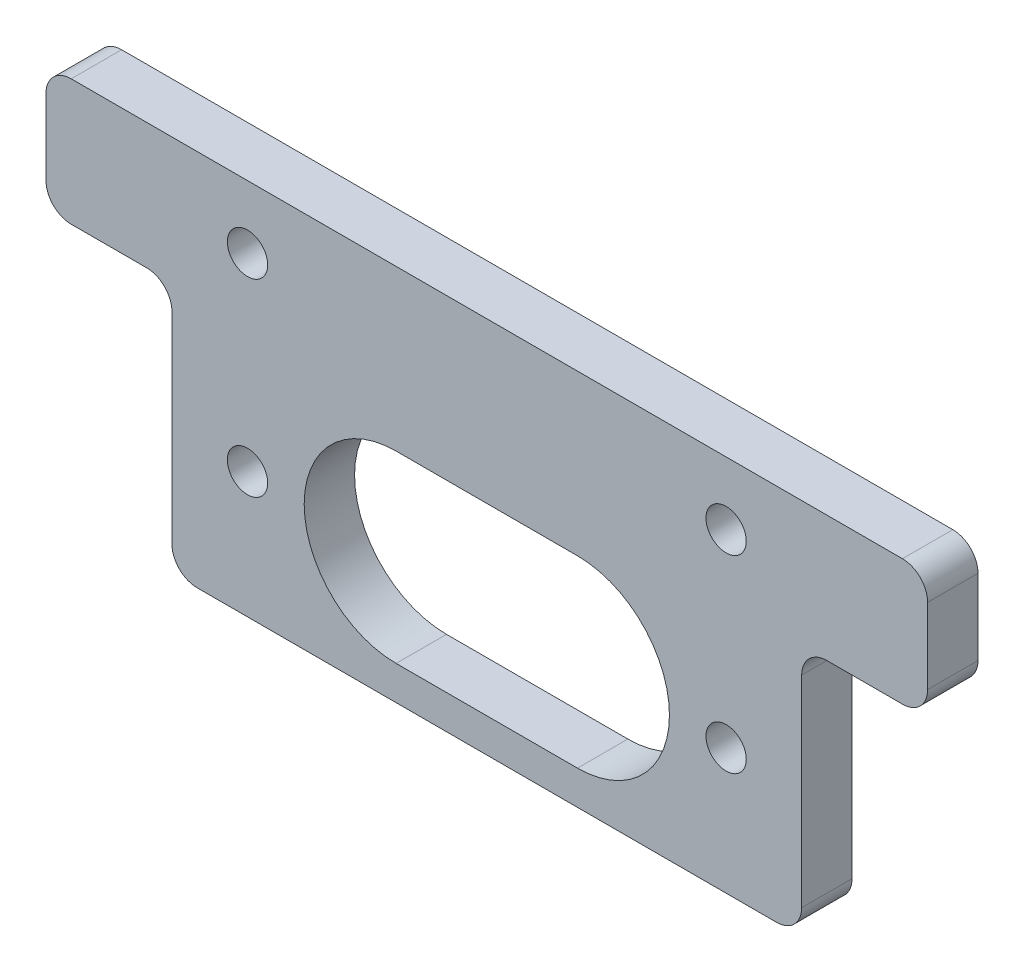
SolidWorks part; units mm, degrees
material "ABS PC"
ref_plane "前视基准面" through (0, 0, 0) normal (0, 0, 1) x (1, 0, 0)
ref_plane "上视基准面" through (0, 0, 0) normal (0, 1, 0) x (1, 0, 0)
ref_plane "右视基准面" through (0, 0, 0) normal (1, 0, 0) x (0, 0, -1)
sketch "草图1" plane through (0, 0, 0) normal (0, 0, 1) x (1, 0, 0)
  line L0 (-25, 0) -> (25, 0)
  line L1 (25, 0) -> (25, 20)
  line L2 (25, 20) -> (35, 20)
  line L3 (35, 20) -> (35, 30)
  line L4 (35, 30) -> (-35, 30)
  line L5 (-35, 30) -> (-35, 20)
  line L6 (-35, 20) -> (-25, 20)
  line L7 (-25, 20) -> (-25, 0)
  line L8 (0, 0) -> (0, 32.7266) construction
  dimension "D1" = 70
  dimension "D2" = 50
  dimension "D3" = 10
  dimension "D4" = 20
extrude "凸台-拉伸1" add sketch "草图1" along normal blind 4
sketch "草图2" plane through (0, 0, 4) normal (0, 0, 1) x (1, 0, 0)
  line L0 (0, 0) -> (0, 38.3649) construction
  line L1 (-25, 0) -> (25, 0) construction
  line L2 (19, 10) -> (19, 25) construction
  line L3 (25, 0) -> (25, 20) construction
  circle A0 centre (19, 10) radius 1.6
  circle A1 centre (19, 25) radius 1.6
  circle A2 centre (-19, 10) radius 1.6
  circle A3 centre (-19, 25) radius 1.6
  dimension "D1" = 3.2
  dimension "D3" = 15
  dimension "D4" = 10
  dimension "D5" = 6
  dimension "D2" = 2
extrude "切除-拉伸1" cut sketch "草图2" against normal through all
sketch "草图3" plane through (0, 0, 4) normal (0, 0, 1) x (1, 0, 0)
  line L0 (-7.2, 10) -> (7.2, 10) construction
  line L1 (-7.2, 16.8) -> (7.2, 16.8) construction
  line L2 (-7.2, 3.2) -> (7.2, 3.2) construction
  line L3 (-25, 0) -> (25, 0) construction
  line L4 (0, 0) -> (0, 32.0857) construction
  line L5 (19, 10) -> (-19, 10) construction
  line L6 (-7.2, 17.3) -> (7.2, 17.3)
  line L7 (-7.2, 2.7) -> (7.2, 2.7)
  arc A0 (-7.2, 16.8) -> (-7.2, 3.2) centre (-7.2, 10) ccw construction
  arc A1 (7.2, 3.2) -> (7.2, 16.8) centre (7.2, 10) ccw construction
  arc A2 (7.2, 2.7) -> (7.2, 17.3) centre (7.2, 10) ccw
  arc A3 (-7.2, 17.3) -> (-7.2, 2.7) centre (-7.2, 10) ccw
  point P2 (0, 10)
  dimension "D1" = 6.8
  dimension "D2" = 14.4
  dimension "D3" = 0.5
extrude "切除-拉伸2" cut sketch "草图3" against normal through all
fillet "圆角1" radius 2 8 edges at (35, 30, 2) (-35, 30, 2) (35, 20, 2) (25, 0, 2) (-25, 0, 2) (-35, 20, 2) (-25, 20, 2) (25, 20, 2)
